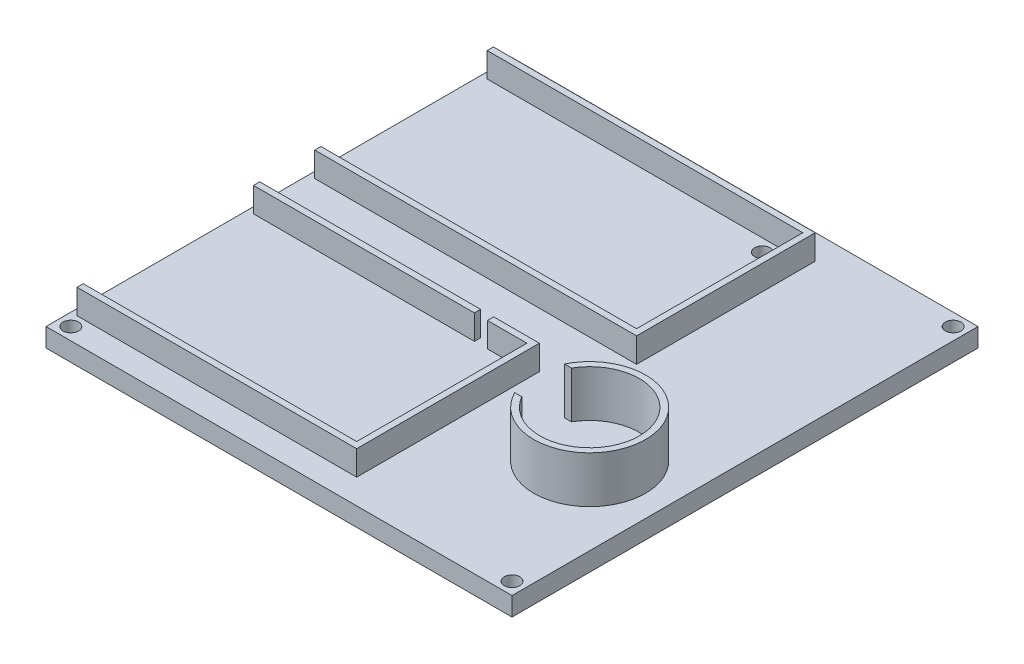
SolidWorks part; units mm, degrees
ref_plane "Front Plane" through (0, 0, 0) normal (0, 0, 1) x (1, 0, 0)
ref_plane "Top Plane" through (0, 0, 0) normal (0, 1, 0) x (1, 0, 0)
ref_plane "Right Plane" through (0, 0, 0) normal (1, 0, 0) x (0, 0, -1)
sketch "Sketch1" plane through (0, 0, 0) normal (0, 1, 0) x (1, 0, 0)
  line L1 (-75, 75) -> (75, 75)
  line L2 (-75, 75) -> (-75, -75)
  line L3 (-75, -75) -> (75, -75)
  line L4 (75, 75) -> (75, -75)
  dimension "D1" = 150
  dimension "D2" = 150
  dimension "D3" = 75
  dimension "D4" = 75
extrude "Boss-Extrude1" add sketch "Sketch1" along normal blind 6
sketch "Sketch2" plane through (0, 6, 0) normal (0, 1, 0) x (1, 0, 0)
  line L0 (-75, 75) -> (-75, -75) construction
  line L1 (-73, 67) -> (30.6, 67)
  line L2 (-75, 67) -> (-75, 9.5)
  line L3 (-75, 9.5) -> (30.6, 9.5)
  line L4 (30.6, 67) -> (30.6, 9.5)
  line L5 (75, 75) -> (-75, 75) construction
  line L6 (-75, -8.2) -> (-1.92, -8.2)
  line L7 (-75, -8.2) -> (-75, -67)
  line L8 (-75, -67) -> (17, -67)
  line L9 (17, -8.2) -> (17, -67)
  line L10 (-75, -75) -> (75, -75) construction
  line L11 (-73, 65) -> (28.6, 65)
  line L12 (28.6, 65) -> (28.6, 11.5)
  line L13 (-73, 11.5) -> (28.6, 11.5)
  line L14 (-73, 65) -> (-73, 11.5)
  line L15 (-73, -10.2) -> (-1.92, -10.2)
  line L16 (15, -10.2) -> (15, -65)
  line L17 (-73, -65) -> (15, -65)
  line L18 (-73, -10.2) -> (-73, -65)
  line L19 (2.3, -10.2) -> (2.3, -8.2)
  line L20 (-1.92, -8.2) -> (-1.92, -10.2)
  line L21 (2.3, -8.2) -> (17, -8.2)
  line L22 (2.3, -10.2) -> (15, -10.2)
  line L23 (-75, -8.2) -> (17, -8.2) construction
  line L24 (-73, -8.2) -> (-73, -67)
  line L25 (-73, -10.2) -> (15, -10.2) construction
  line L26 (-73, 67) -> (-73, 9.5)
  line L27 (75, -75) -> (75, 75) construction
  line L28 (-75, 67) -> (30.6, 67) construction
  circle A0 centre (50, -25) radius 16
  circle A1 centre (50, -25) radius 18
  dimension "D11" = 25
  dimension "D13" = 32
  dimension "D1" = 57.5
  dimension "D2" = 105.6
  dimension "D3" = 58.8
  dimension "D4" = 92
  dimension "D5" = 8
  dimension "D6" = 8
  dimension "D9" = 12.7
  dimension "D10" = 4.22
  dimension "D12" = 50
  dimension "D7" = 2
  dimension "D8" = 2
  dimension "D14" = 2
extrude "Boss-Extrude2" add sketch "Sketch2" along normal blind 7.94 contours L1 L26 L11 L12 L13 L3 L4 | L6 L24 L15 L20 | L17 L24 L8 L9 L21 L19 L22 L16 | A1 A0
sketch "Sketch3" plane through (0, 13.94, 0) normal (0, 1, 0) x (1, 0, 0)
  circle A0 centre (50, -25) radius 16 construction
  circle A1 centre (50, -25) radius 18
  circle A2 centre (50, -25) radius 18
  circle A3 centre (50, -25) radius 16
  dimension "D1" = 0
extrude "Boss-Extrude3" add sketch "Sketch3" along normal blind 7.06
sketch "Sketch4" plane through (0, 6, 0) normal (0, 1, 0) x (1, 0, 0)
sketch "Sketch5" plane through (0, 6, 0) normal (0, 1, 0) x (1, 0, 0)
  line L1 (75, 75) -> (-75, 75) construction
  line L2 (-75, 75) -> (-75, -75) construction
  line L3 (0, -3.3) -> (0, 3.3) construction
  line L4 (-3.3, 0) -> (3.3, 0) construction
  line L5 (-73, 11.5) -> (28.6, 11.5) construction
  line L6 (28.6, 65) -> (28.6, 11.5) construction
  line L7 (-73, 65) -> (28.6, 65) construction
  circle A0 centre (-71, 71) radius 2.5
  circle A4 centre (19.6, 61) radius 2.5
  circle A5 centre (24.6, 15.5) radius 2.5
  circle A6 centre (71, 71) radius 2.5
  circle A7 centre (71, -71) radius 2.5
  circle A8 centre (-71, -71) radius 2.5
  dimension "D1" = 5
  dimension "D4" = 5
  dimension "D7" = 5
  dimension "D2" = 4
  dimension "D3" = 4
  dimension "D5" = 4
  dimension "D6" = 4
  dimension "D8" = 5
  dimension "D9" = 4
extrude "Cut-Extrude1" cut sketch "Sketch5" against normal through all
sketch "Sketch6" plane through (0, 21, 0) normal (0, 1, 0) x (1, 0, 0)
  line L0 (63.8564, -17) -> (66.1245, -17)
  line L1 (33.8755, -17) -> (36.1436, -17)
  line L2 (33.8755, -17) -> (33.8755, -33)
  line L3 (33.8755, -33) -> (36.1436, -33)
  line L4 (66.1245, -17) -> (66.1245, -33)
  line L5 (63.8564, -33) -> (66.1245, -33)
  circle A2 centre (50, -25) radius 18 construction
  circle A3 centre (50, -25) radius 18 construction
  circle A4 centre (50, -25) radius 16 construction
  circle A5 centre (50, -25) radius 16
  circle A6 centre (50, -25) radius 18
  point P8 (65.5189, -15.8807)
  point P9 (34.3938, -33.9691)
  circle M1 centre (50, -25) radius 18
  circle M2 centre (50, -25) radius 16
  dimension "D1" = 16
extrude "Cut-Extrude2" cut sketch "Sketch6" against normal up to surface (15 mm away) contours L2 M1 | L2 L3 L1 M2 up to face at (-71, 6, 68.5)
